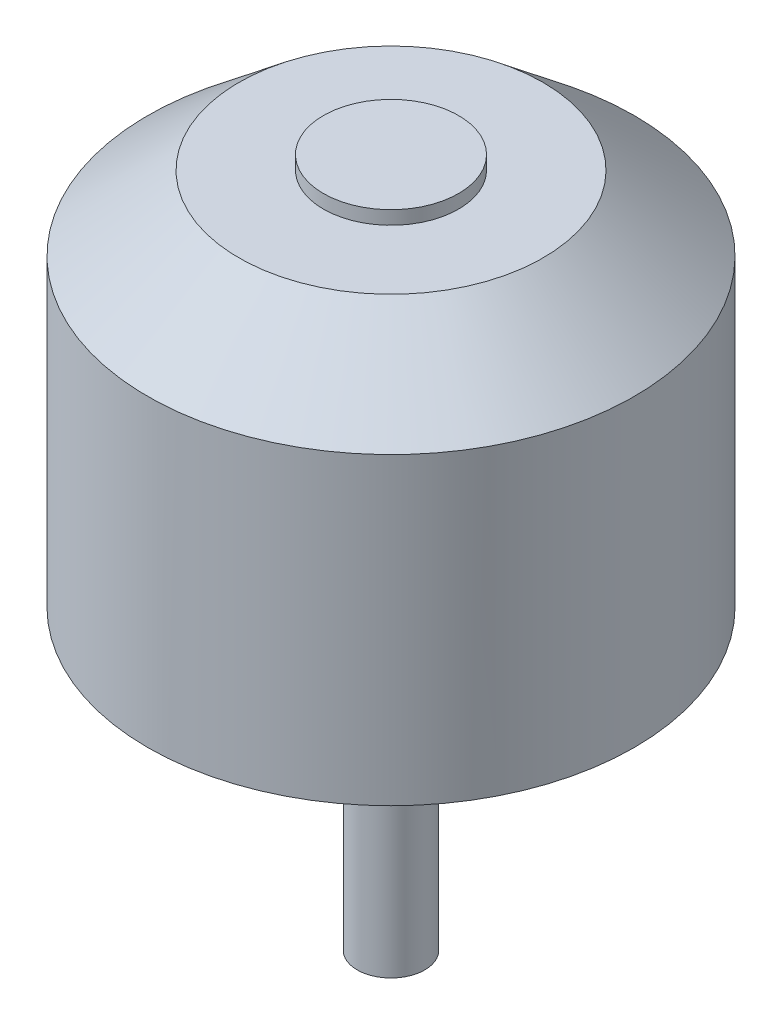
SolidWorks part; units mm, degrees
ref_plane "Alzado" through (0, 0, 0) normal (0, 0, 1) x (1, 0, 0)
ref_plane "Planta" through (0, 0, 0) normal (0, 1, 0) x (1, 0, 0)
ref_plane "Vista lateral" through (0, 0, 0) normal (1, 0, 0) x (0, 0, -1)
sketch "Croquis1" plane through (0, 0, 0) normal (0, 1, 0) x (1, 0, 0)
  circle A0 centre (0, 0) radius 18
  dimension "D1" = 36
extrude "Saliente-Extruir1" add sketch "Croquis1" along normal blind 29
sketch "Croquis2" plane through (0, 0, 0) normal (0, -1, 0) x (1, 0, 0)
  circle A0 centre (0, 0) radius 2.5
  dimension "D1" = 5
extrude "Saliente-Extruir2" add sketch "Croquis2" along normal blind 22
sketch "Croquis3" plane through (0, 29, 0) normal (0, 1, 0) x (1, 0, 0)
  circle A0 centre (0, 0) radius 5
  circle A1 centre (0, 0) radius 18
  circle A2 centre (0, 0) radius 18 construction
  dimension "D1" = 10
extrude "Cortar-Extruir1" cut sketch "Croquis3" against normal blind 1
sketch "Croquis4" plane through (0, 0, 0) normal (0, 0, 1) x (1, 0, 0)
  line L0 (-18, 22.5) -> (-11.25, 28)
  line L1 (-18, 28) -> (-18, 0) construction
  line L2 (18, 28) -> (-18, 28) construction
  line L3 (-11.25, 28) -> (-18, 28)
  line L4 (-18, 28) -> (-18, 22.5)
  line L5 (-18, 0) -> (18, 0) construction
  line L7 (0, 0) -> (0, 29) construction
  line L8 (5, 29) -> (-5, 29) construction
  point P19 (0, 0)
  dimension "D1" = 22.5
  dimension "D2" = 11.25
revolve "Cortar-Revolución1" cut sketch "Croquis4" angle 360 about L7
